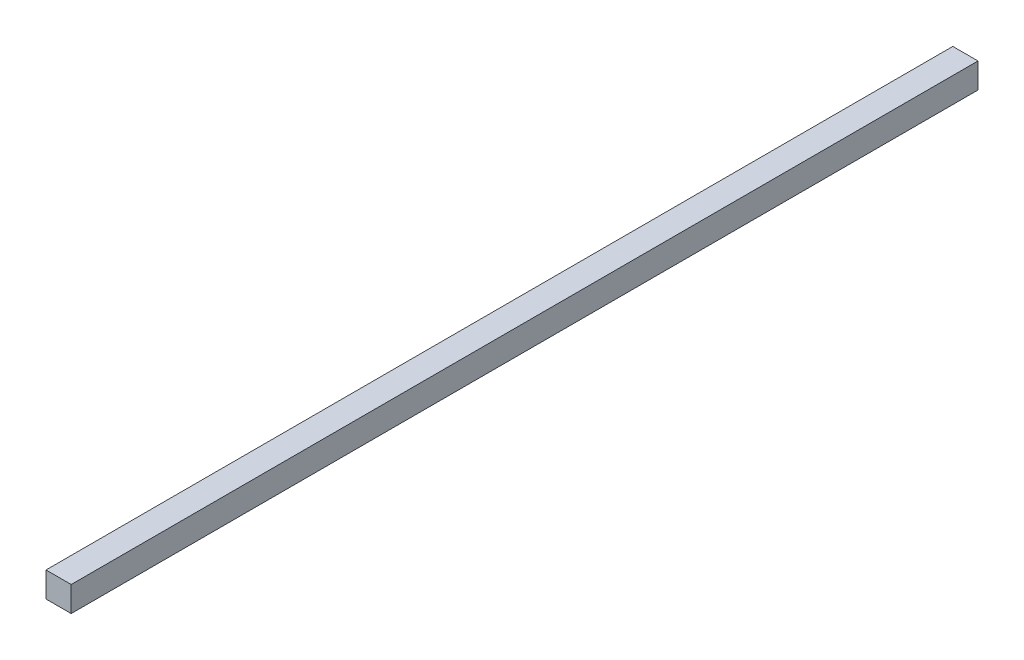
SolidWorks part; units mm, degrees
material "6061 Alloy"
ref_plane "Front Plane" through (0, 0, 0) normal (0, 0, 1) x (1, 0, 0)
ref_plane "Top Plane" through (0, 0, 0) normal (0, 1, 0) x (1, 0, 0)
ref_plane "Right Plane" through (0, 0, 0) normal (1, 0, 0) x (0, 0, -1)
sketch "Sketch1" plane through (0, 0, 0) normal (0, 0, 1) x (1, 0, 0)
  line L1 (-12.7, -12.7) -> (12.7, -12.7)
  line L2 (-12.7, -12.7) -> (-12.7, 12.7)
  line L3 (-12.7, 12.7) -> (12.7, 12.7)
  line L4 (12.7, -12.7) -> (12.7, 12.7)
  line L5 (-12.7, -12.7) -> (12.7, 12.7) construction
  line L6 (-12.7, 12.7) -> (12.7, -12.7) construction
  point P0 (0, 0)
  dimension "D1" = 25.4
  dimension "D2" = 25.4
extrude "Boss-Extrude1" add sketch "Sketch1" along normal blind 914.4
